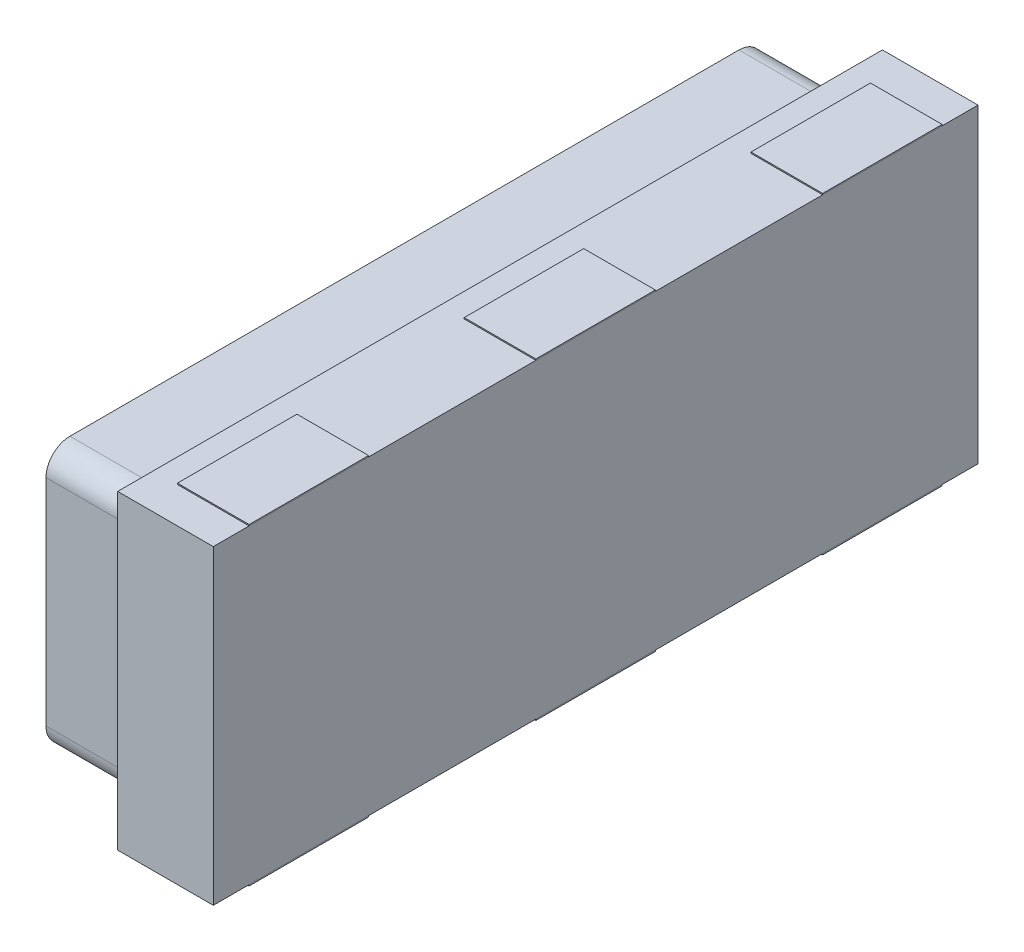
SolidWorks part; units mm, degrees
ref_plane "Спереди" through (0, 0, 0) normal (0, 0, 1) x (1, 0, 0)
ref_plane "Сверху" through (0, 0, 0) normal (0, 1, 0) x (1, 0, 0)
ref_plane "Справа" through (0, 0, 0) normal (1, 0, 0) x (0, 0, -1)
sketch "Эскиз1" plane through (0, 0, 0) normal (1, 0, 0) x (0, 0, -1)
  line L1 (1.6, 0.65) -> (-1.6, 0.65)
  line L2 (1.6, 0.65) -> (1.6, -0.65)
  line L3 (1.6, -0.65) -> (-1.6, -0.65)
  line L4 (-1.6, 0.65) -> (-1.6, -0.65)
  line L5 (1.6, 0.65) -> (-1.6, -0.65) construction
  line L6 (1.6, -0.65) -> (-1.6, 0.65) construction
  point P0 (0, 0)
  dimension "D1" = 1.3
  dimension "D2" = 3.2
extrude "Бобышка-Вытянуть1" add sketch "Эскиз1" along normal blind 0.4
sketch "Эскиз2" plane through (0, 0, 0) normal (-1, 0, 0) x (0, 0, 1)
  line L0 (-1.6, -0.65) -> (-1.6, 0.65) construction
  line L1 (-1.4, 0.55) -> (1.4, 0.55)
  line L2 (-1.5, 0.45) -> (-1.5, -0.45)
  line L3 (-1.4, -0.55) -> (1.4, -0.55)
  line L4 (1.5, 0.45) -> (1.5, -0.45)
  line L5 (-1.5, 0.55) -> (1.5, -0.55) construction
  line L6 (-1.5, -0.55) -> (1.5, 0.55) construction
  line L7 (-1.6, 0.65) -> (1.6, 0.65) construction
  arc A0 (1.4, 0.55) -> (1.5, 0.45) centre (1.4, 0.45) cw
  arc A1 (1.4, -0.55) -> (1.5, -0.45) centre (1.4, -0.45) ccw
  arc A2 (-1.5, -0.45) -> (-1.4, -0.55) centre (-1.4, -0.45) ccw
  arc A3 (-1.4, 0.55) -> (-1.5, 0.45) centre (-1.4, 0.45) ccw
  point P0 (0, 0)
  dimension "D3" = 0.1
  dimension "D1" = 0.1
  dimension "D2" = 0.1
extrude "Бобышка-Вытянуть2" add sketch "Эскиз2" along normal blind 0.4 separate body
sketch "Эскиз3" plane through (0.4, 0, 0) normal (1, 0, 0) x (0, 0, -1)
  line L1 (-0.25, 0.655) -> (0.25, 0.655)
  line L2 (-0.25, 0.655) -> (-0.25, -0.655)
  line L3 (-0.25, -0.655) -> (0.25, -0.655)
  line L4 (0.25, 0.655) -> (0.25, -0.655)
  line L5 (-0.25, 0.655) -> (0.25, -0.655) construction
  line L6 (-0.25, -0.655) -> (0.25, 0.655) construction
  line L7 (0.95, 0.655) -> (1.45, 0.655)
  line L8 (0.95, 0.655) -> (0.95, -0.655)
  line L9 (0.95, -0.655) -> (1.45, -0.655)
  line L10 (1.45, 0.655) -> (1.45, -0.655)
  line L11 (0.95, 0.655) -> (1.45, -0.655) construction
  line L12 (0.95, -0.655) -> (1.45, 0.655) construction
  line L13 (-1.45, 0.655) -> (-0.95, 0.655)
  line L14 (-1.45, 0.655) -> (-1.45, -0.655)
  line L15 (-1.45, -0.655) -> (-0.95, -0.655)
  line L16 (-0.95, 0.655) -> (-0.95, -0.655)
  line L17 (-1.45, 0.655) -> (-0.95, -0.655) construction
  line L18 (-1.45, -0.655) -> (-0.95, 0.655) construction
  point P0 (0, 0)
  point P6 (1.2, 0)
  point P11 (-1.2, 0)
  dimension "D1" = 0.5
  dimension "D2" = 0.5
  dimension "D3" = 0.5
  dimension "D4" = 1.2
  dimension "D5" = 1.2
  dimension "D6" = 1.31
extrude "Бобышка-Вытянуть3" add sketch "Эскиз3" against normal blind 0.3 separate body
